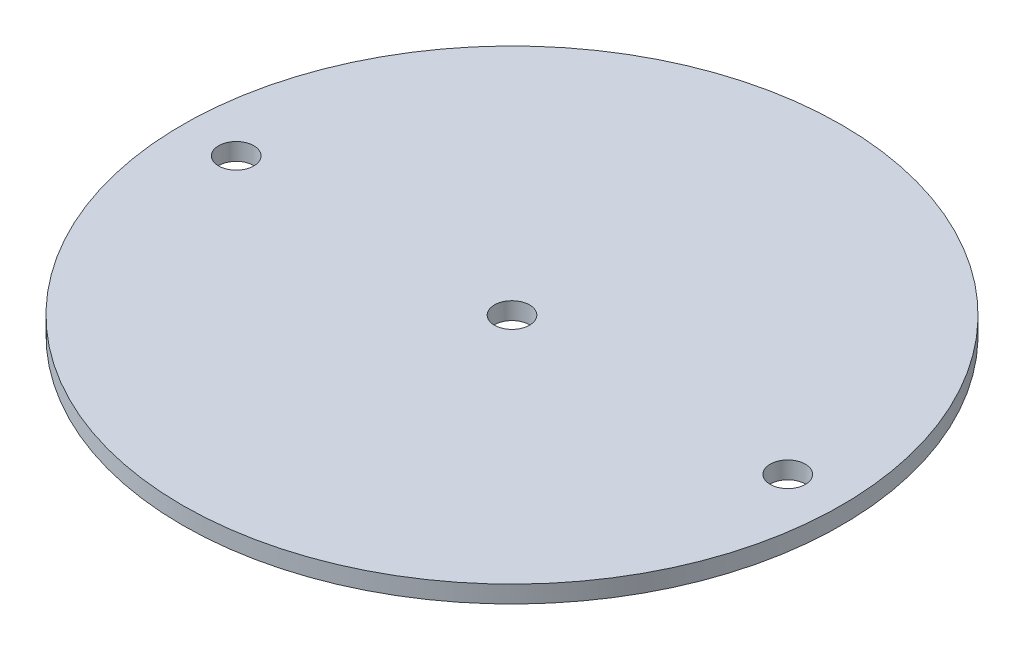
SolidWorks part; units mm, degrees
ref_plane "Front Plane" through (0, 0, 0) normal (0, 0, 1) x (1, 0, 0)
ref_plane "Top Plane" through (0, 0, 0) normal (0, 1, 0) x (1, 0, 0)
ref_plane "Right Plane" through (0, 0, 0) normal (1, 0, 0) x (0, 0, -1)
sketch "Sketch2" plane through (0, 0, 0) normal (0, 1, 0) x (1, 0, 0)
  line L0 (-50.8, 0) -> (50.8, 0) construction
  circle A0 centre (0, 0) radius 60.706
  circle A1 centre (-50.8, 0) radius 3.2385
  circle A2 centre (50.8, 0) radius 3.2385
  circle A3 centre (0, 0) radius 3.2385
  point P6 (0, 0)
  dimension "D1" = 121.412
  dimension "D3" = 6.477
  dimension "D4" = 6.477
  dimension "D2" = 101.6
extrude "Boss-Extrude1" add sketch "Sketch2" along normal blind 3.175
